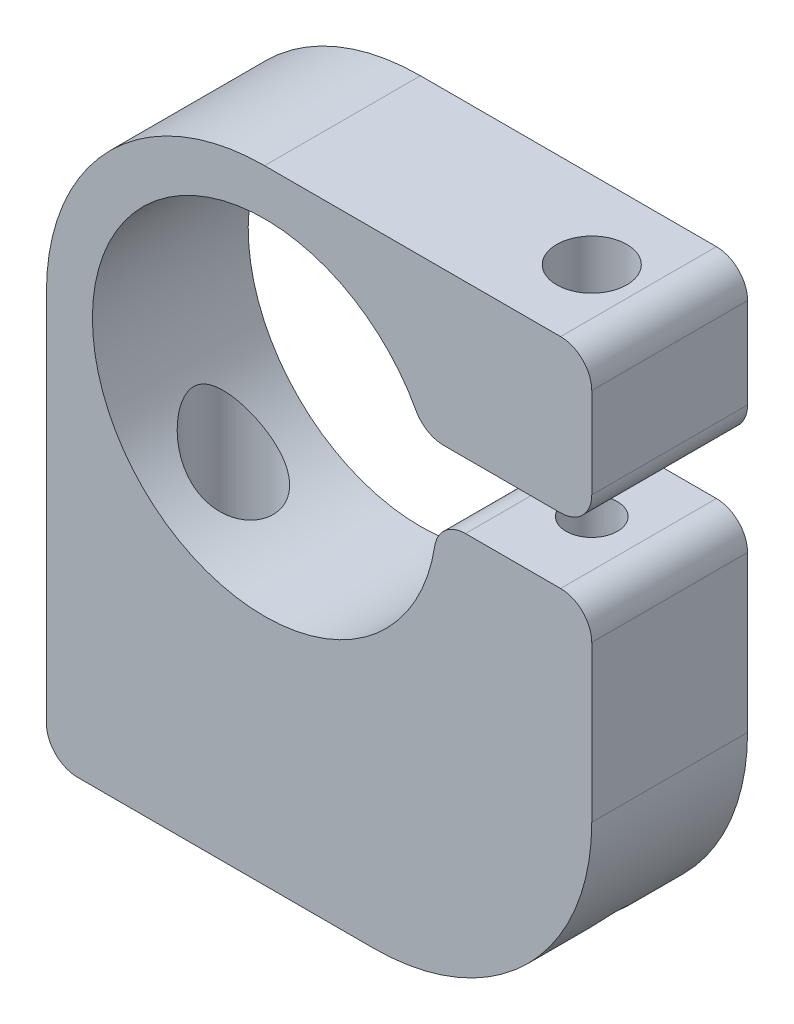
SolidWorks part; units mm, degrees
material "Сплав 2024"
ref_plane "Спереди" through (0, 0, 0) normal (0, 0, 1) x (1, 0, 0)
ref_plane "Сверху" through (0, 0, 0) normal (0, 1, 0) x (1, 0, 0)
ref_plane "Справа" through (0, 0, 0) normal (1, 0, 0) x (0, 0, -1)
sketch "Эскиз1" plane through (0, 0, 0) normal (0, 0, 1) x (1, 0, 0)
  line L0 (10.2207, 4.2) -> (21, 4.2)
  line L1 (0, 14) -> (21, 14)
  line L2 (-14, 0) -> (-14, -26)
  line L3 (-14, -26) -> (7, -26)
  line L4 (21, 14) -> (21, 4.2)
  line L5 (21, 0) -> (11.05, 0)
  line L6 (21, 0) -> (21, -12)
  arc A0 (10.2207, 4.2) -> (11.05, 0) centre (0, 0) ccw
  arc A1 (0, 14) -> (-14, 0) centre (0, 0) ccw
  arc A2 (7, -26) -> (21, -12) centre (7, -12) ccw
  dimension "D1" = 22.1
  dimension "D2" = 28
  dimension "D7" = 28
  dimension "D3" = 35
  dimension "D4" = 4.2
  dimension "D5" = 9.8
  dimension "D6" = 26
extrude "Бобышка-Вытянуть1" add sketch "Эскиз1" along normal blind 10
sketch "Эскиз2" plane through (0, 14, 0) normal (0, 1, 0) x (1, 0, 0)
  line L0 (21, -5) -> (1.7357, -5) construction
  line L1 (21, -10) -> (21, 0) construction
  line L2 (16, 0) -> (16, -10) construction
  line L3 (21, 0) -> (0, 0) construction
  line L4 (21, -10) -> (0, -10) construction
  dimension "D1" = 5
hole_wizard "Отверстие с зазором M41" positions "Эскиз4" profile "Эскиз3" hole size "M4" standard "Ansi Metric"
sketch "Эскиз4" plane through (0, 14, 0) normal (0, 1, 0) x (1, 0, 0)
  line L0 (16, 0) -> (16, -10) construction
  point P0 (16, -5)
sketch "Эскиз3" plane through (16, 14, 5) normal (1, 0, 0) x (0, 0, 1)
  line L0 (0, 0) -> (0, 9.8)
  line L1 (0, 9.8) -> (2.25, 9.8)
  line L2 (2.25, 9.8) -> (2.25, 0)
  line L5 (2.25, 0) -> (0, 0)
  line L11 (0, -6.35) -> (0, 107.95) construction
  dimension "Диаметр сквозного отверстия" = 4.5
  dimension "Глубина сквозного отверстия" = 9.8
hole_wizard "Отверстие обработанное метчиком M4x0.71" positions "Эскиз6" profile "Эскиз5" tap size "M4x0.7" standard "Ansi Metric" end condition through all
sketch "Эскиз6" plane through (0, 0, 0) normal (0, 1, 0) x (1, 0, 0)
  line L0 (16, 0) -> (16, -10) construction
  point P0 (16, -5)
sketch "Эскиз5" plane through (16, 0, 5) normal (1, 0, 0) x (0, 0, 1)
  line L0 (0, 0) -> (0, 26)
  line L1 (0, 26) -> (1.65, 26)
  line L2 (1.65, 26) -> (1.65, 0)
  line L5 (1.65, 0) -> (0, 0)
  line L11 (0, -6.35) -> (0, 107.95) construction
  dimension "Диаметр проходного сверла" = 3.3
  dimension "Глубина проходного сверла" = 26
cosmetic thread "Отверстие резьбы1" parameters "D2"=4
sketch "Эскиз7" plane through (0, -26, 0) normal (0, -1, 0) x (1, 0, 0)
  line L0 (-14, 5) -> (0, 5) construction
  line L1 (-14, 10) -> (-14, 0) construction
  line L2 (-7, 10) -> (-7, 0) construction
  line L3 (-14, 10) -> (7, 10) construction
  line L4 (-14, 0) -> (7, 0) construction
  dimension "D1" = 7
hole_wizard "Отверстие обработанное метчиком 1/4-201" positions "Эскиз9" profile "Эскиз8" tap size "1/4-20" standard "Ansi Inch"
sketch "Эскиз9" plane through (0, -26, 0) normal (0, -1, 0) x (-1, 0, 0)
  line L0 (14, -5) -> (0, -5) construction
  point P0 (7, -5)
sketch "Эскиз8" plane through (-7, -26, 5) normal (1, 0, 0) x (0, 0, -1)
  line L0 (0, 0) -> (0, 17.45)
  line L1 (0, 17.45) -> (2.5527, 17.45)
  line L2 (2.5527, 17.45) -> (2.5527, 0)
  line L5 (2.5527, 0) -> (0, 0)
  line L11 (0, -6.35) -> (0, 107.95) construction
  dimension "Диаметр проходного сверла" = 5.1054
  dimension "Глубина проходного сверла" = 17.45
cosmetic thread "Отверстие резьбы2" parameters "D2"=6.35
fillet "Скругление1" radius 2 6 edges at (-14, -26, 5) (21, 14, 5) (21, 4.2, 5) (21, 0, 5) (11.05, 0, 5) (10.2207, 4.2, 5)
fillet "Скругление2" [suppressed] radius 0.5
fillet "Скругление3" [suppressed] radius 0.5
sketch "Эскиз10" plane through (0, 0, 0) normal (0, 0, 1) x (1, 0, 0)
  line L0 (-12, -26) -> (7, -26) construction
  line L1 (-14, 0) -> (-14, -24) construction
  point P0 (-14, -26)
